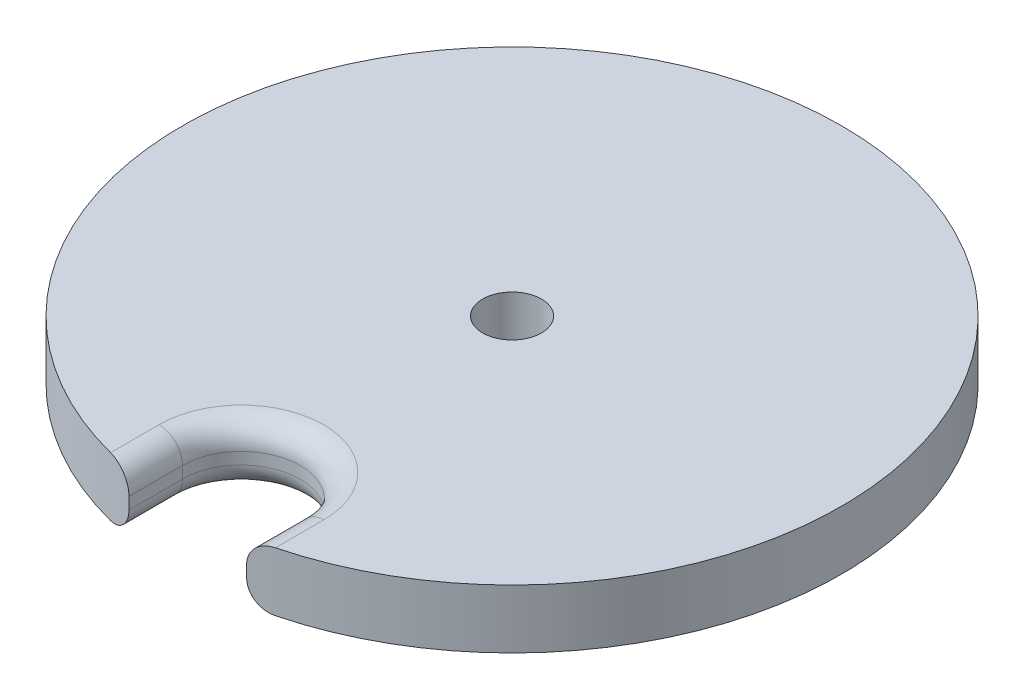
SolidWorks part; units mm, degrees
ref_plane "Front Plane" through (0, 0, 0) normal (0, 0, 1) x (1, 0, 0)
ref_plane "Top Plane" through (0, 0, 0) normal (0, 1, 0) x (1, 0, 0)
ref_plane "Right Plane" through (0, 0, 0) normal (1, 0, 0) x (0, 0, -1)
sketch "Sketch2" plane through (0, 0, 0) normal (0, 1, 0) x (1, 0, 0)
  circle A0 centre (0, 0) radius 35.56
  dimension "D1" = 71.12
extrude "Boss-Extrude1" add sketch "Sketch2" along normal blind 6.35
sketch "Sketch4" plane through (0, 6.35, 0) normal (0, 1, 0) x (1, 0, 0)
  line L0 (-6.35, -29.21) -> (-6.35, -34.9884)
  line L1 (6.35, -29.21) -> (6.35, -34.9884)
  arc A0 (6.35, -29.21) -> (-6.35, -29.21) centre (0, -29.21) ccw
  circle A1 centre (0, 0) radius 35.56 construction
  dimension "D1" = 12.7
extrude "Shock Cord hole" cut sketch "Sketch4" against normal through all and the other way through all flip side to cut
fillet "Fillet1" radius 2.54 6 edges at (-6.35, 6.35, 32.0992) (0, 6.35, 22.86) (6.35, 6.35, 32.0992) (-6.35, 0, 32.0992) (0, 0, 22.86) (6.35, 0, 32.0992)
sketch "Sketch17" plane through (0, 0, 0) normal (0, -1, 0) x (1, 0, 0)
  line L0 (0, 0) -> (35.56, 0) construction
sketch "Sketch18" plane through (0, 0, 0) normal (0, -1, 0) x (1, 0, 0)
  circle A0 centre (0, 0) radius 3.175
  dimension "D1" = 6.35
extrude "Cut-Extrude1" cut sketch "Sketch18" against normal through all
